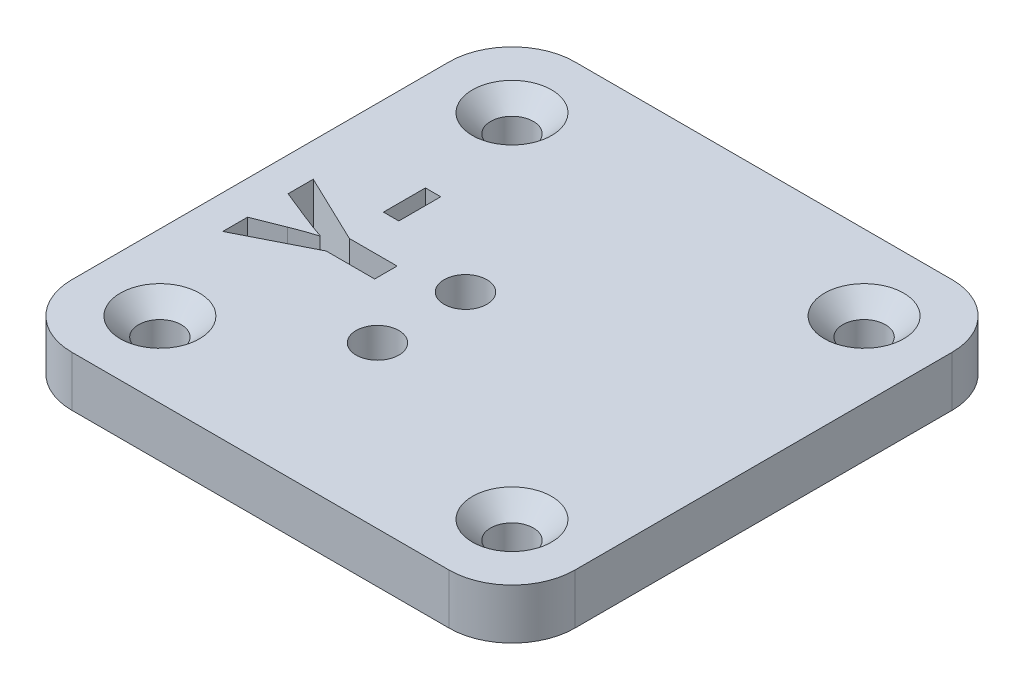
SolidWorks part; units mm, degrees
ref_plane "Front Plane" through (0, 0, 0) normal (0, 0, 1) x (1, 0, 0)
ref_plane "Top Plane" through (0, 0, 0) normal (0, 1, 0) x (1, 0, 0)
ref_plane "Right Plane" through (0, 0, 0) normal (1, 0, 0) x (0, 0, -1)
sketch "Sketch1" plane through (0, 0, 0) normal (0, 1, 0) x (1, 0, 0)
  line L1 (-15, -20) -> (15, -20)
  line L2 (-20, -15) -> (-20, 15)
  line L3 (-15, 20) -> (15, 20)
  line L4 (20, -15) -> (20, 15)
  line L5 (-20, -20) -> (20, 20) construction
  line L6 (-20, 20) -> (20, -20) construction
  arc A0 (20, -15) -> (15, -20) centre (15, -15) cw
  arc A1 (-15, -20) -> (-20, -15) centre (-15, -15) cw
  arc A2 (20, 15) -> (15, 20) centre (15, 15) ccw
  arc A3 (-15, 20) -> (-20, 15) centre (-15, 15) ccw
  point P0 (0, 0)
  dimension "D3" = 5
  dimension "D1" = 40
  dimension "D2" = 40
extrude "Boss-Extrude1" add sketch "Sketch1" along normal blind 4
sketch "Sketch2" plane through (0, 4, 0) normal (0, 1, 0) x (1, 0, 0)
  line L1 (-14, -14) -> (14, -14) construction
  line L2 (-14, -14) -> (-14, 14) construction
  line L3 (-14, 14) -> (14, 14) construction
  line L4 (14, -14) -> (14, 14) construction
  line L5 (-14, -14) -> (14, 14) construction
  line L6 (-14, 14) -> (14, -14) construction
  point P0 (0, 0)
  dimension "D1" = 28
  dimension "D2" = 28
hole_wizard "CSK for M3 Countersunk Flat Head Screw1" positions "3DSketch1" profile "Sketch3" countersink size "M3" standard "DIN" end condition through all
sketch3d "3DSketch1"
  point P0 (-14, 4, -14)
  point P3 (14, 4, -14)
  point P6 (14, 4, 14)
  point P9 (-14, 4, 14)
sketch "Sketch3" plane through (-14, 4, -14) normal (1, 0, 0) x (0, 0, 1)
  line L0 (0, 0) -> (0, 4)
  line L1 (0, 4) -> (1.7, 4)
  line L2 (1.7, 4) -> (1.7, 1.45)
  line L3 (1.7, 1.45) -> (3.15, 0)
  line L5 (3.15, 0) -> (0, 0)
  line L6 (-1.7, 1.45) -> (-3.15, 0) construction
  line L11 (0, -6.35) -> (0, 107.95) construction
  dimension "Thru Hole Dia." = 3.4
  dimension "Thru Hole Depth" = 4
  dimension "Near C'Sink Dia." = 6.3
  dimension "Near C'Sink Angle" = 90
sketch "Sketch4" plane through (0, 0, 0) normal (0, 1, 0) x (1, 0, 0)
  line L0 (0, 0) -> (0, -8.708) construction
  arc A0 (-5.25, -0.1977) -> (-1.75, -0.1977) centre (-3.5, -0.1977) ccw construction
  arc A1 (-1.75, -0.1977) -> (-5.25, -0.1977) centre (-3.5, -0.1977) ccw construction
  arc A2 (-5.25, -7.1977) -> (-1.75, -7.1977) centre (-3.5, -7.1977) ccw construction
  arc A3 (-1.75, -7.1977) -> (-5.25, -7.1977) centre (-3.5, -7.1977) ccw construction
  arc A4 (-5.25, -0.1977) -> (-1.75, -0.1977) centre (-3.5, -0.1977) ccw construction
  arc A5 (-1.75, -0.1977) -> (-5.25, -0.1977) centre (-3.5, -0.1977) ccw construction
  arc A6 (-5.25, -7.1977) -> (-1.75, -7.1977) centre (-3.5, -7.1977) ccw construction
  arc A7 (-1.75, -7.1977) -> (-5.25, -7.1977) centre (-3.5, -7.1977) ccw construction
  arc A9 (1.75, -0.1977) -> (5.25, -0.1977) centre (3.5, -0.1977) cw construction
  arc A10 (5.25, -0.1977) -> (1.75, -0.1977) centre (3.5, -0.1977) cw construction
  arc A11 (5.25, -7.1977) -> (1.75, -7.1977) centre (3.5, -7.1977) cw construction
  arc A12 (1.75, -7.1977) -> (5.25, -7.1977) centre (3.5, -7.1977) cw construction
hole_wizard "CSK for M3 Countersunk Flat Head Screw2" positions "Sketch5" profile "Sketch6" countersink size "M3" standard "DIN" end condition through all
sketch "Sketch5" plane through (0, 0, 0) normal (0, -1, 0) x (-1, 0, 0)
  point P18 (3.5, -0.1977)
  point P21 (3.5, -7.1977)
sketch "Sketch6" plane through (-3.5, 0, 0.1977) normal (1, 0, 0) x (0, 0, -1)
  line L0 (0, 0) -> (0, 4)
  line L1 (0, 4) -> (1.7, 4)
  line L2 (1.7, 4) -> (1.7, 1.45)
  line L3 (1.7, 1.45) -> (3.15, 0)
  line L5 (3.15, 0) -> (0, 0)
  line L6 (-1.7, 1.45) -> (-3.15, 0) construction
  line L11 (0, -6.35) -> (0, 107.95) construction
  dimension "Thru Hole Dia." = 3.4
  dimension "Thru Hole Depth" = 4
  dimension "Near C'Sink Dia." = 6.3
  dimension "Near C'Sink Angle" = 90
sketch "Sketch7" plane through (0, 4, 0) normal (0, 1, 0) x (1, 0, 0)
  line L0 (-8, 20) -> (-8, -20) construction
  line L1 (15, 20) -> (-15, 20) construction
  line L2 (0, 0) -> (0, 20) construction
  line L3 (-15, -20) -> (15, -20) construction
  text T0 "-Y" font "@Adobe Gothic Std B" height in points 30
  dimension "D2" = 8
extrude "Cut-Extrude1" cut sketch "Sketch7" against normal up to surface (4 mm away) up to face at (-3.5, 0, -2.9523)
